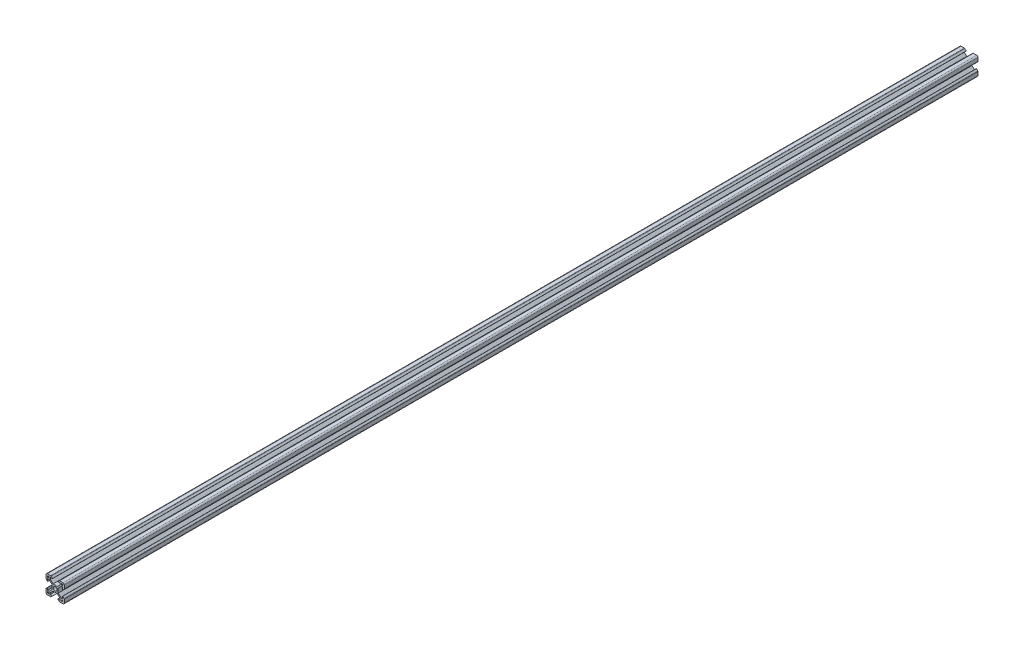
SolidWorks part; units mm, degrees
ref_plane "Front Plane" through (0, 0, 0) normal (0, 0, 1) x (1, 0, 0)
ref_plane "Top Plane" through (0, 0, 0) normal (0, 1, 0) x (1, 0, 0)
ref_plane "Right Plane" through (0, 0, 0) normal (1, 0, 0) x (0, 0, -1)
sketch "Sketch2" plane through (0, 0, 0) normal (0, 0, 1) x (1, 0, 0)
  line L0 (-8.2, 2.89) -> (-8.2, 5.5)
  line L1 (-2.1, 0) -> (-10, 0) construction
  line L2 (0, 2.1) -> (0, 10) construction
  line L3 (-4.9072, 10) -> (-8.5, 10)
  line L4 (-10, 4.9072) -> (-10, 8.5)
  line L5 (-2.1, 0) -> (-3.4, 0) construction
  line L6 (0, 2.1) -> (0, 3.4) construction
  line L7 (0, 3.4) -> (-2.3393, 3.4)
  line L8 (-3.4, 0) -> (-3.4, 2.3393)
  line L9 (-2.89, 8.2) -> (-5.5, 8.2)
  line L10 (-6.57, 8.2) -> (-6.57, 7.66)
  line L11 (-8.2, 6.57) -> (-7.66, 6.57)
  line L12 (-5.5, 8.2) -> (-5.5, 6.5607)
  line L13 (-6.5607, 5.5) -> (-8.2, 5.5)
  line L14 (-8.2, 8.2) -> (-1.4849, 1.4849) construction
  line L15 (-6.5607, 5.5) -> (-3.4, 2.3393)
  line L16 (-5.5, 6.5607) -> (-2.3393, 3.4)
  line L17 (-7.66, 6.57) -> (-6.57, 7.66)
  line L18 (-8.7303, 7.6697) -> (-0.5303, -0.5303) construction
  line L19 (-7.6697, 8.7303) -> (0.5303, 0.5303) construction
  line L20 (-8.2, 8.2) -> (0, 0) construction
  line L21 (-8.2, 6.57) -> (-8.2, 8.2)
  line L22 (-8.2, 0) -> (-8.2, 8.2) construction
  line L23 (-6.57, 8.2) -> (-8.2, 8.2)
  line L24 (0, 8.2) -> (-8.2, 8.2) construction
  line L25 (-10, 0) -> (-10, 10) construction
  line L26 (0, 10) -> (-10, 10) construction
  line L27 (-2.89, 8.31) -> (-2.89, 8.2)
  line L29 (-8.31, 2.89) -> (-8.2, 2.89)
  line L30 (-4.3486, 9.7686) -> (-2.89, 8.31)
  line L31 (-8.31, 2.89) -> (-9.7686, 4.3486)
  arc A0 (0, 2.1) -> (-2.1, 0) centre (0, 0) ccw
  arc A1 (-10, 8.5) -> (-8.5, 10) centre (-8.5, 8.5) cw
  arc A2 (-9.7686, 4.3486) -> (-10, 4.9072) centre (-9.21, 4.9072) cw
  arc A3 (-4.3486, 9.7686) -> (-4.9072, 10) centre (-4.9072, 9.21) ccw
  point P29 (-10, 10)
  point P39 (-10, 4.58)
  point P42 (-4.58, 10)
  dimension "D3" = 2.1
  dimension "D15" = 1.5
  dimension "D22" = 0.79
  dimension "D1" = 10
  dimension "D2" = 10
  dimension "D4" = 1.8
  dimension "D5" = 3.43
  dimension "D6" = 3.43
  dimension "D7" = 0.54
  dimension "D8" = 0.54
  dimension "D9" = 1.07
  dimension "D10" = 1.07
  dimension "D11" = 3.4
  dimension "D12" = 3.4
  dimension "D16" = 7.11
  dimension "D17" = 0.11
  dimension "D18" = 1.69
  dimension "D19" = 0.11
  dimension "D20" = 7.11
  dimension "D21" = 1.69
  dimension "D13" = 0.75
  dimension "D14" = 0.75
sketch "Sketch6" plane through (0, 0, 0) normal (0, 0, 1) x (1, 0, 0)
  line L0 (-3.4, 0) -> (-3.4, 2.3393) construction
  line L1 (-6.5607, 5.5) -> (-3.4, 2.3393) construction
  line L2 (-6.5607, 5.5) -> (-8.2, 5.5) construction
  line L3 (-8.2, 2.89) -> (-8.2, 5.5) construction
  line L4 (-8.31, 2.89) -> (-8.2, 2.89) construction
  line L5 (-7.66, 6.57) -> (-6.57, 7.66)
  line L6 (-6.57, 7.66) -> (-6.57, 8.2)
  line L7 (-6.57, 8.2) -> (-8.2, 8.2)
  line L8 (-8.2, 8.2) -> (-8.2, 6.57)
  line L9 (-8.2, 6.57) -> (-7.66, 6.57)
  line L10 (-7.66, 6.57) -> (-6.57, 7.66)
  line L11 (-6.57, 7.66) -> (-6.57, 8.2)
  line L12 (-6.57, 8.2) -> (-8.2, 8.2)
  line L13 (-8.2, 8.2) -> (-8.2, 6.57)
  line L14 (-8.2, 6.57) -> (-7.66, 6.57)
  line L15 (-8.31, 2.89) -> (-9.7686, 4.3486) construction
  line L16 (-10, 4.9072) -> (-10, 8.5) construction
  line L17 (-4.9072, 10) -> (-8.5, 10) construction
  line L18 (-4.3486, 9.7686) -> (-2.89, 8.31) construction
  line L19 (-2.89, 8.31) -> (-2.89, 8.2) construction
  line L20 (-2.89, 8.2) -> (-5.5, 8.2) construction
  line L21 (-5.5, 8.2) -> (-5.5, 6.5607) construction
  line L22 (-5.5, 6.5607) -> (-2.3393, 3.4) construction
  line L23 (0, 3.4) -> (-2.3393, 3.4) construction
  line L24 (-3.4, -2.3393) -> (-3.4, 2.3393)
  line L25 (-6.5607, 5.5) -> (-3.4, 2.3393)
  line L26 (-6.5607, 5.5) -> (-8.2, 5.5)
  line L27 (-8.2, 2.89) -> (-8.2, 5.5)
  line L28 (-8.31, 2.89) -> (-8.2, 2.89)
  line L29 (-8.31, 2.89) -> (-9.7686, 4.3486)
  line L30 (-10, 4.9072) -> (-10, 8.5)
  line L31 (-4.9072, 10) -> (-8.5, 10)
  line L32 (-4.3486, 9.7686) -> (-2.89, 8.31)
  line L33 (-2.89, 8.31) -> (-2.89, 8.2)
  line L34 (-2.89, 8.2) -> (-5.5, 8.2)
  line L35 (-5.5, 8.2) -> (-5.5, 6.5607)
  line L36 (-5.5, 6.5607) -> (-2.3393, 3.4)
  line L37 (2.3393, 3.4) -> (-2.3393, 3.4)
  line L38 (0, 2.1) -> (0, 10) construction
  line L39 (-2.1, 0) -> (-10, 0) construction
  line L40 (0, 2.1) -> (0, 10) construction
  line L41 (-2.1, 0) -> (-10, 0) construction
  line L42 (2.1, 0) -> (10, 0) construction
  line L43 (5.5, 6.5607) -> (2.3393, 3.4)
  line L44 (5.5, 8.2) -> (5.5, 6.5607)
  line L45 (2.89, 8.2) -> (5.5, 8.2)
  line L46 (2.89, 8.31) -> (2.89, 8.2)
  line L47 (4.3486, 9.7686) -> (2.89, 8.31)
  line L48 (4.9072, 10) -> (8.5, 10)
  line L49 (10, 4.9072) -> (10, 8.5)
  line L50 (8.31, 2.89) -> (9.7686, 4.3486)
  line L51 (8.31, 2.89) -> (8.2, 2.89)
  line L52 (8.2, 2.89) -> (8.2, 5.5)
  line L53 (6.5607, 5.5) -> (8.2, 5.5)
  line L54 (6.5607, 5.5) -> (3.4, 2.3393)
  line L55 (3.4, -2.3393) -> (3.4, 2.3393)
  line L56 (8.2, 6.57) -> (7.66, 6.57)
  line L57 (8.2, 8.2) -> (8.2, 6.57)
  line L58 (6.57, 8.2) -> (8.2, 8.2)
  line L59 (6.57, 7.66) -> (6.57, 8.2)
  line L60 (7.66, 6.57) -> (6.57, 7.66)
  line L61 (0, -2.1) -> (0, -10) construction
  line L62 (7.66, -6.57) -> (6.57, -7.66)
  line L63 (6.57, -7.66) -> (6.57, -8.2)
  line L64 (6.57, -8.2) -> (8.2, -8.2)
  line L65 (8.2, -8.2) -> (8.2, -6.57)
  line L66 (8.2, -6.57) -> (7.66, -6.57)
  line L67 (6.5607, -5.5) -> (3.4, -2.3393)
  line L68 (6.5607, -5.5) -> (8.2, -5.5)
  line L69 (8.2, -2.89) -> (8.2, -5.5)
  line L70 (8.31, -2.89) -> (8.2, -2.89)
  line L71 (8.31, -2.89) -> (9.7686, -4.3486)
  line L72 (10, -4.9072) -> (10, -8.5)
  line L73 (4.9072, -10) -> (8.5, -10)
  line L74 (4.3486, -9.7686) -> (2.89, -8.31)
  line L75 (2.89, -8.31) -> (2.89, -8.2)
  line L76 (2.89, -8.2) -> (5.5, -8.2)
  line L77 (5.5, -8.2) -> (5.5, -6.5607)
  line L78 (5.5, -6.5607) -> (2.3393, -3.4)
  line L79 (2.3393, -3.4) -> (-2.3393, -3.4)
  line L80 (-5.5, -6.5607) -> (-2.3393, -3.4)
  line L81 (-5.5, -8.2) -> (-5.5, -6.5607)
  line L82 (-2.89, -8.2) -> (-5.5, -8.2)
  line L83 (-2.89, -8.31) -> (-2.89, -8.2)
  line L84 (-4.3486, -9.7686) -> (-2.89, -8.31)
  line L85 (-4.9072, -10) -> (-8.5, -10)
  line L86 (-10, -4.9072) -> (-10, -8.5)
  line L87 (-8.31, -2.89) -> (-9.7686, -4.3486)
  line L88 (-8.31, -2.89) -> (-8.2, -2.89)
  line L89 (-8.2, -2.89) -> (-8.2, -5.5)
  line L90 (-6.5607, -5.5) -> (-8.2, -5.5)
  line L91 (-6.5607, -5.5) -> (-3.4, -2.3393)
  line L92 (-8.2, -6.57) -> (-7.66, -6.57)
  line L93 (-8.2, -8.2) -> (-8.2, -6.57)
  line L94 (-6.57, -8.2) -> (-8.2, -8.2)
  line L95 (-6.57, -7.66) -> (-6.57, -8.2)
  line L96 (-7.66, -6.57) -> (-6.57, -7.66)
  arc A0 (0, 2.1) -> (-2.1, 0) centre (0, 0) ccw construction
  arc A1 (-10, 4.9072) -> (-9.7686, 4.3486) centre (-9.21, 4.9072) ccw construction
  arc A2 (-8.5, 10) -> (-10, 8.5) centre (-8.5, 8.5) ccw construction
  arc A3 (-4.3486, 9.7686) -> (-4.9072, 10) centre (-4.9072, 9.21) ccw construction
  circle A4 centre (0, 0) radius 2.1
  arc A5 (-10, 4.9072) -> (-9.7686, 4.3486) centre (-9.21, 4.9072) ccw
  arc A6 (-8.5, 10) -> (-10, 8.5) centre (-8.5, 8.5) ccw
  arc A7 (-4.3486, 9.7686) -> (-4.9072, 10) centre (-4.9072, 9.21) ccw
  arc A8 (4.3486, 9.7686) -> (4.9072, 10) centre (4.9072, 9.21) cw
  arc A9 (8.5, 10) -> (10, 8.5) centre (8.5, 8.5) cw
  arc A10 (10, 4.9072) -> (9.7686, 4.3486) centre (9.21, 4.9072) cw
  arc A11 (10, -4.9072) -> (9.7686, -4.3486) centre (9.21, -4.9072) ccw
  arc A12 (8.5, -10) -> (10, -8.5) centre (8.5, -8.5) ccw
  arc A13 (4.3486, -9.7686) -> (4.9072, -10) centre (4.9072, -9.21) ccw
  arc A14 (-4.3486, -9.7686) -> (-4.9072, -10) centre (-4.9072, -9.21) cw
  arc A15 (-8.5, -10) -> (-10, -8.5) centre (-8.5, -8.5) cw
  arc A16 (-10, -4.9072) -> (-9.7686, -4.3486) centre (-9.21, -4.9072) cw
  point P85 (3.4, 0)
  dimension "D1" = 0
extrude "Boss-Extrude1" add sketch "Sketch6" against normal blind 1000
